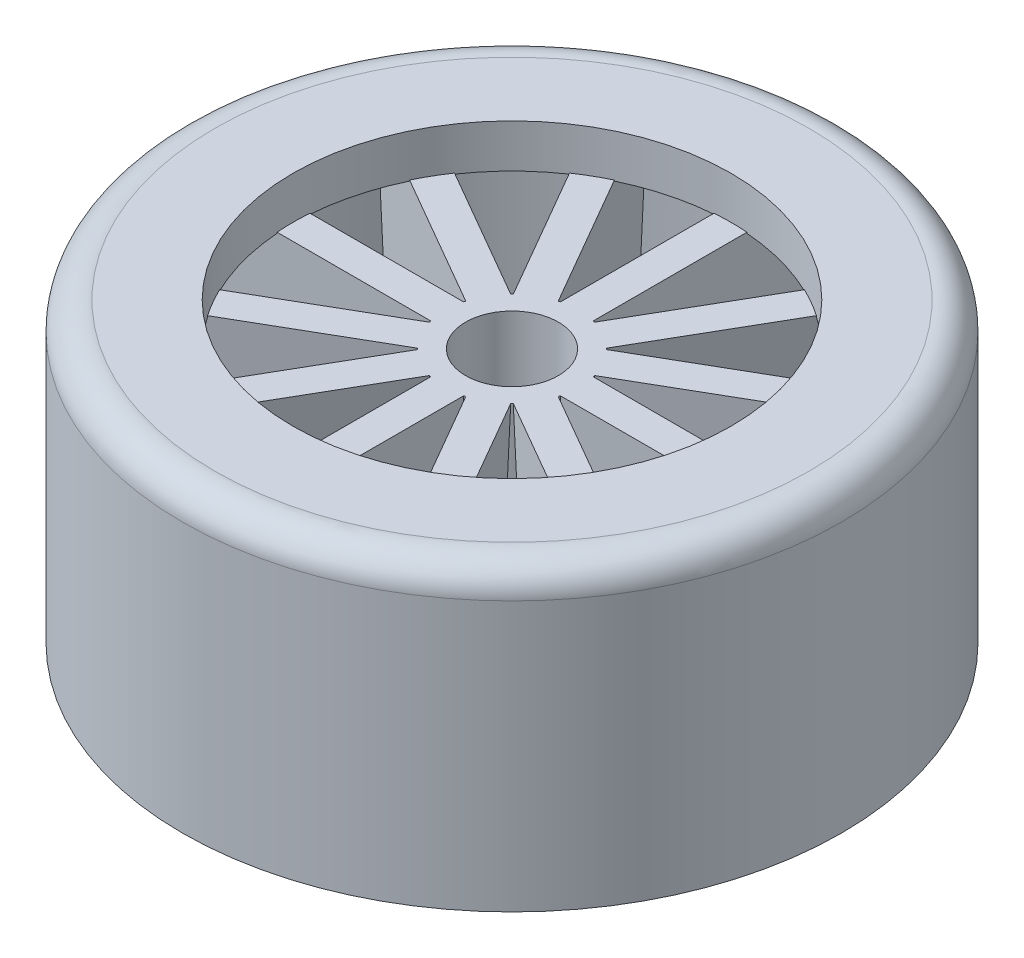
SolidWorks part; units mm, degrees
material "1.0035 (S185)"
ref_plane "Alzado" through (0, 0, 0) normal (0, 0, 1) x (1, 0, 0)
ref_plane "Planta" through (0, 0, 0) normal (0, 1, 0) x (1, 0, 0)
ref_plane "Vista lateral" through (0, 0, 0) normal (1, 0, 0) x (0, 0, -1)
sketch "Croquis3" plane through (0, 0, 0) normal (0, 0, 1) x (1, 0, 0)
  line L0 (-18.65, 21.6) -> (-24.75, 21.6)
  line L1 (-25.2846, 25.3) -> (-18.65, 25.3)
  line L2 (-28.05, 22.928) -> (-28.05, 0)
  line L3 (-26.25, 20.1) -> (-26.25, 6.3)
  line L4 (-26.25, 6.3) -> (-26.25, 0)
  line L5 (0, 23.5294) -> (0, 0) construction
  line L6 (-26.25, 0) -> (-28.05, 0)
  line L7 (-5.7, 21.6787) -> (-5.55, 6.2787)
  line L8 (-3.95, 21.6787) -> (-3.95, 6.2787)
  line L9 (-3.95, 6.2787) -> (-5.55, 6.2787)
  line L10 (-5.7, 21.6787) -> (-3.95, 21.6787)
  line L15 (-18.65, 25.3) -> (-18.65, 21.6)
  arc A0 (-26.25, 20.1) -> (-24.75, 21.6) centre (-24.75, 20.1) cw
  arc A2 (-28.05, 22.928) -> (-25.2846, 25.3) centre (-25.65, 22.928) cw
  point P12 (-26.25, 0.6599)
  point P13 (0, 0)
  dimension "D24" = 2.4
  dimension "D1" = 1.5
  dimension "D3" = 1.75
  dimension "D4" = 28.05
  dimension "D5" = 25.3
  dimension "D6" = 1.8
  dimension "D7" = 1.6
  dimension "D8" = 3.95
  dimension "D25" = 9.4
  dimension "D26" = 3.7
revolve "Revolución1" add sketch "Croquis3" angle 360 about L5
ref_plane "Plano1" through (0, 21.6787, 0) normal (0, 1, 0) x (1, 0, 0)
sketch "Croquis7" plane through (0, 21.6787, 0) normal (0, 1, 0) x (1, 0, 0)
  line L1 (1.4, 5.4067) -> (1.4, 26.8822)
  line L2 (-1.4, 5.4067) -> (-1.4, 26.8822)
  line L6 (-1.4, 26.8822) -> (1.4, 26.8822)
  line L7 (-1.4, 5.4067) -> (1.4, 5.4067)
sketch "Croquis9" plane through (0, 0, 0) normal (0, 1, 0) x (1, 0, 0)
  line L0 (0, 4.7898) -> (0, 27.3457) construction
  line L1 (0.6, 4.7898) -> (0.6, 27.3457)
  line L2 (-0.6, 4.7898) -> (-0.6, 27.3457)
  line L3 (-0.6, 4.7898) -> (0.6, 4.7898)
  line L4 (-0.6, 27.3457) -> (0.6, 27.3457)
  dimension "D1" = 0.6
  dimension "D2" = 0.6
loft "Recubrir3" add profiles "Croquis9", "Croquis7"
pattern_circular "MatrizC1" count 12 over 360 about axis through (0, 0, 0) along (0, 1, 0) of "Recubrir3"
sketch "Croquis12" plane through (0, 0, 0) normal (0, -1, 0) x (1, 0, 0)
  circle A0 centre (0, 0) radius 26.25
extrude "Cortar-Extruir1" cut sketch "Croquis12" against normal up to surface (6.2787 mm away) up to face at (0, 6.2787, 3.95)
